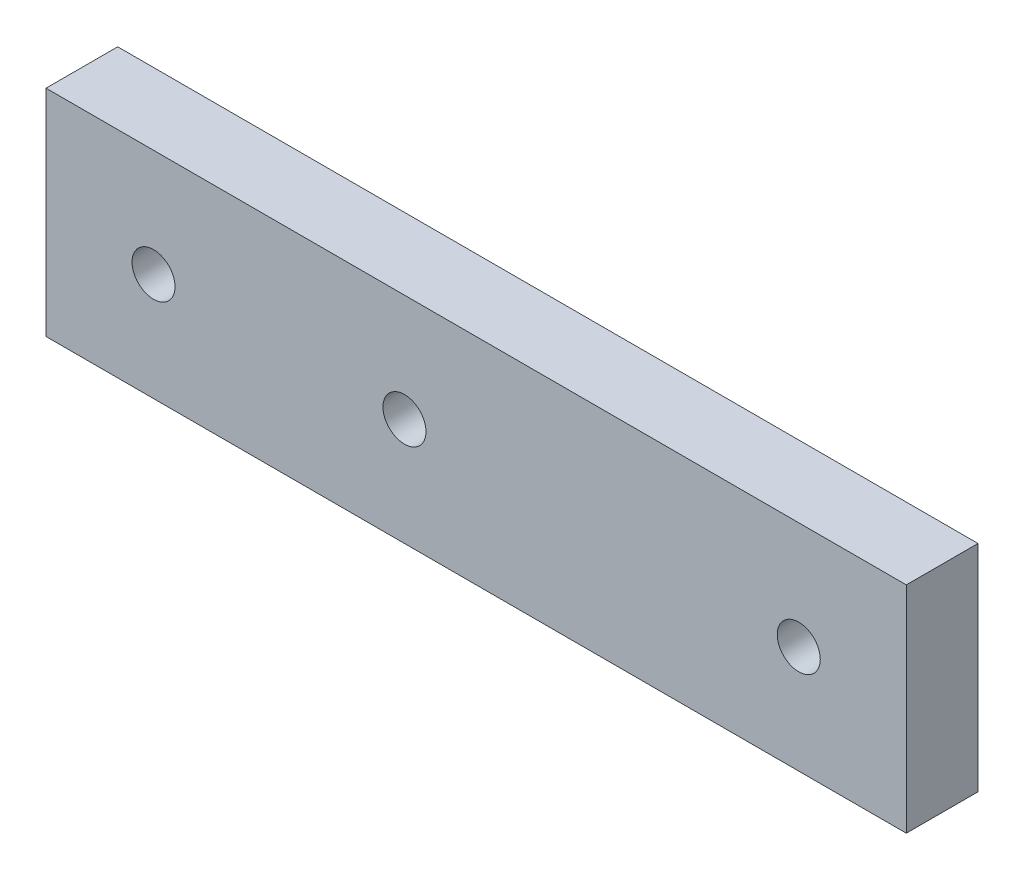
SolidWorks part; units mm, degrees
ref_plane "Front Plane" through (0, 0, 0) normal (0, 0, 1) x (1, 0, 0)
ref_plane "Top Plane" through (0, 0, 0) normal (0, 1, 0) x (1, 0, 0)
ref_plane "Right Plane" through (0, 0, 0) normal (1, 0, 0) x (0, 0, -1)
sketch "Sketch2" plane through (0, 0, 0) normal (0, 0, 1) x (1, 0, 0)
  line L1 (0, 0) -> (-60, 0)
  line L2 (0, 0) -> (0, 15)
  line L3 (0, 15) -> (-60, 15)
  line L4 (-60, 0) -> (-60, 15)
  circle A0 centre (-52.5, 7.5) radius 1.5
  circle A1 centre (-35, 7.5) radius 1.5
  circle A2 centre (-7.5, 7.5) radius 1.5
  dimension "D3" = 3
  dimension "D4" = 3
  dimension "D5" = 3
  dimension "D6" = 7.5
  dimension "D7" = 7.5
  dimension "D8" = 7.5
  dimension "D9" = 7.5
  dimension "D10" = 25
  dimension "D11" = 52.5
  dimension "D1" = 60
  dimension "D2" = 15
extrude "Boss-Extrude1" add sketch "Sketch2" along normal blind 5
